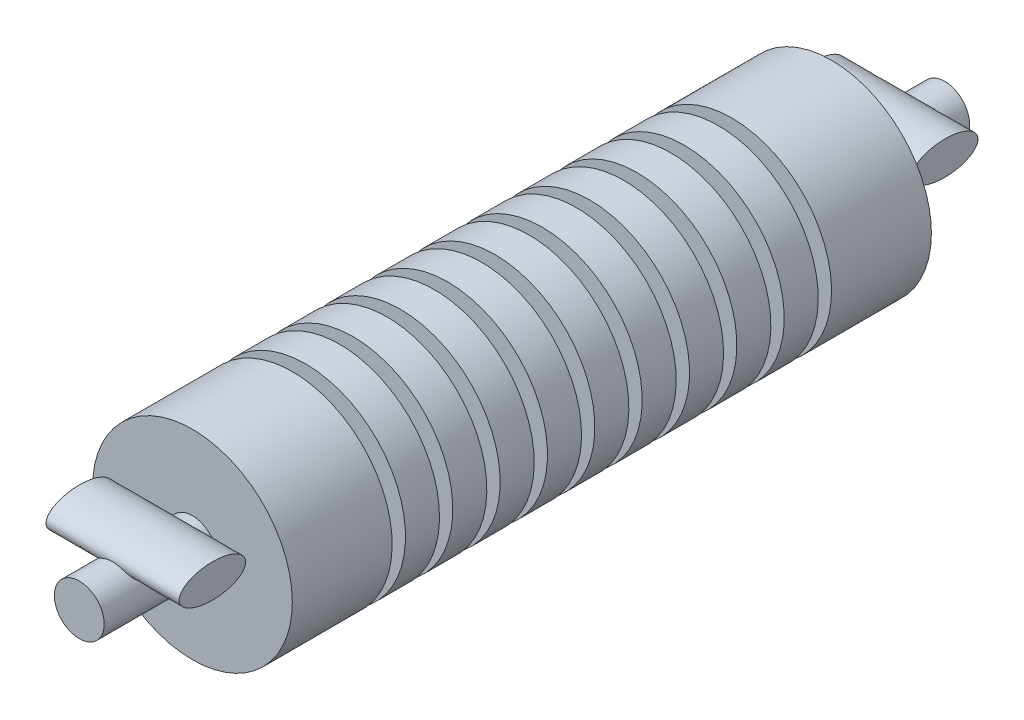
SolidWorks part; units mm, degrees
material "Ceramic Porcelain"
ref_plane "Front Plane" through (0, 0, 0) normal (0, 0, 1) x (1, 0, 0)
ref_plane "Top Plane" through (0, 0, 0) normal (0, 1, 0) x (1, 0, 0)
ref_plane "Right Plane" through (0, 0, 0) normal (1, 0, 0) x (0, 0, -1)
sketch "Sketch1" plane through (0, 0, 0) normal (0, 0, 1) x (1, 0, 0)
  circle A0 centre (0, 0) radius 1.5
  dimension "D1" = 3
extrude "Boss-Extrude1" add sketch "Sketch1" along normal mid plane 9.6
sketch "Sketch2" plane through (0, 0, 0) normal (1, 0, 0) x (0, 0, -1)
  line L0 (4.8, 1.5) -> (-4.8, 1.5) construction
  line L1 (-3.3, 1.5) -> (-3.1, 1.5)
  line L2 (-3.3, 1.5) -> (-3.3, -1.5)
  line L3 (-3.3, -1.5) -> (-3.1, -1.5)
  line L4 (-3.1, 1.5) -> (-3.1, -1.5)
  line L5 (-4.8, -1.5) -> (4.8, -1.5) construction
  line L6 (-4.8, 1.5) -> (-4.8, -1.5) construction
  line L7 (-2.5889, 1.5) -> (-2.3889, 1.5)
  line L8 (-2.5889, 1.5) -> (-2.5889, -1.5)
  line L9 (-2.5889, -1.5) -> (-2.3889, -1.5)
  line L10 (-2.3889, 1.5) -> (-2.3889, -1.5)
  line L11 (-1.8778, 1.5) -> (-1.6778, 1.5)
  line L12 (-1.8778, 1.5) -> (-1.8778, -1.5)
  line L13 (-1.8778, -1.5) -> (-1.6778, -1.5)
  line L14 (-1.6778, 1.5) -> (-1.6778, -1.5)
  line L15 (-1.1667, 1.5) -> (-0.9667, 1.5)
  line L16 (-1.1667, 1.5) -> (-1.1667, -1.5)
  line L17 (-1.1667, -1.5) -> (-0.9667, -1.5)
  line L18 (-0.9667, 1.5) -> (-0.9667, -1.5)
  line L19 (-0.4556, 1.5) -> (-0.2556, 1.5)
  line L20 (-0.4556, 1.5) -> (-0.4556, -1.5)
  line L21 (-0.4556, -1.5) -> (-0.2556, -1.5)
  line L22 (-0.2556, 1.5) -> (-0.2556, -1.5)
  line L23 (0.2556, 1.5) -> (0.4556, 1.5)
  line L24 (0.2556, 1.5) -> (0.2556, -1.5)
  line L25 (0.2556, -1.5) -> (0.4556, -1.5)
  line L26 (0.4556, 1.5) -> (0.4556, -1.5)
  line L27 (0.9667, 1.5) -> (1.1667, 1.5)
  line L28 (0.9667, 1.5) -> (0.9667, -1.5)
  line L29 (0.9667, -1.5) -> (1.1667, -1.5)
  line L30 (1.1667, 1.5) -> (1.1667, -1.5)
  line L31 (1.6778, 1.5) -> (1.8778, 1.5)
  line L32 (1.6778, 1.5) -> (1.6778, -1.5)
  line L33 (1.6778, -1.5) -> (1.8778, -1.5)
  line L34 (1.8778, 1.5) -> (1.8778, -1.5)
  line L35 (2.3889, 1.5) -> (2.5889, 1.5)
  line L36 (2.3889, 1.5) -> (2.3889, -1.5)
  line L37 (2.3889, -1.5) -> (2.5889, -1.5)
  line L38 (2.5889, 1.5) -> (2.5889, -1.5)
  line L39 (3.1, 1.5) -> (3.3, 1.5)
  line L40 (3.1, 1.5) -> (3.1, -1.5)
  line L41 (3.1, -1.5) -> (3.3, -1.5)
  line L42 (3.3, 1.5) -> (3.3, -1.5)
  line L43 (4.8, -1.5) -> (4.8, 1.5) construction
  line L44 (4.8, -1.5) -> (4.8, 1.5) construction
  dimension "D1" = 1.5
  dimension "D2" = 0.2
  dimension "D4" = 1.5
  dimension "D3" = 10
extrude "Cut-Extrude1" cut sketch "Sketch2" against normal through all both and the other way through all
sketch "Sketch3" plane through (0, 0, 0) normal (0, 0, 1) x (1, 0, 0)
  circle A0 centre (0, 0) radius 0.375
  dimension "D1" = 0.75
extrude "Boss-Extrude2" add sketch "Sketch3" along normal mid plane 13
sketch "Sketch4" plane through (0, 0, 0) normal (1, 0, 0) x (0, 0, -1)
  line L0 (-4.8, 0.375) -> (-6.5, 0.375) construction
  line L1 (-6, 0.375) -> (-5, 0.375) construction
  line L2 (-5.5, 0.125) -> (-5.5, 0.625) construction
  line L3 (-6.5, 0.375) -> (-6.5, -0.375) construction
  line L4 (0, 0) -> (0, 1.5) construction
  line L5 (0.2556, 1.5) -> (-0.2556, 1.5) construction
  line L6 (5.5, 0.125) -> (5.5, 0.625) construction
  line L7 (6, 0.375) -> (5, 0.375) construction
  ellipse E0 centre (-5.5, 0.375) end of major axis (-5, 0.375) minor radius 0.25
  ellipse E1 centre (5.5, 0.375) end of major axis (5, 0.375) minor radius 0.25
  dimension "D1" = 1
  dimension "D2" = 0.5
  dimension "D3" = 0.5
extrude "Boss-Extrude3" add sketch "Sketch4" along normal mid plane 2
